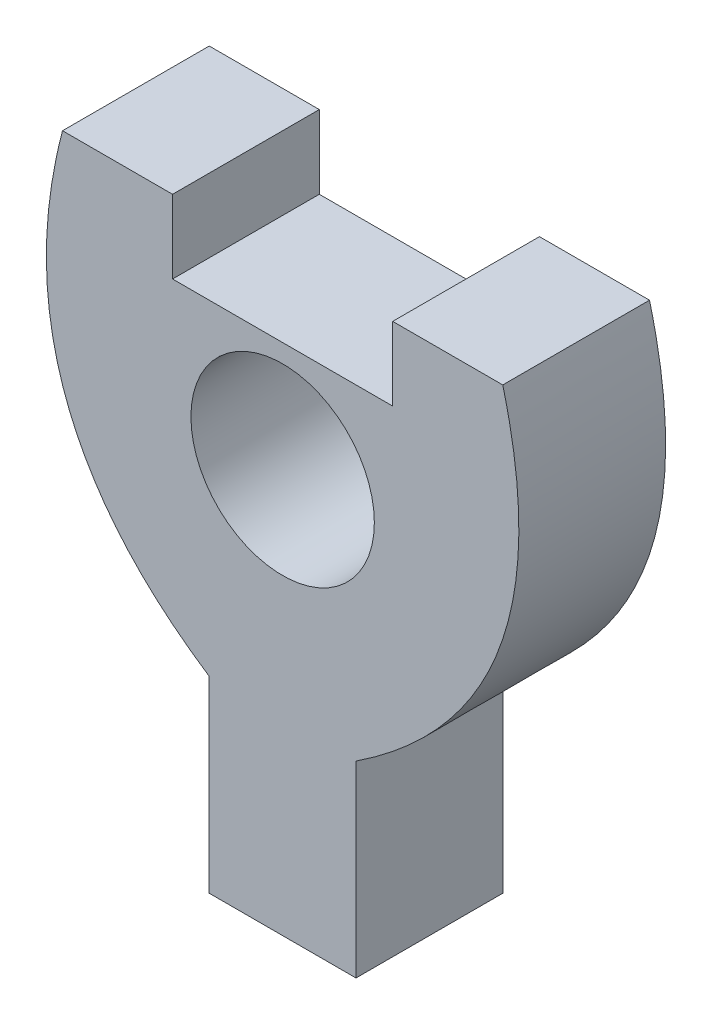
SolidWorks part; units mm, degrees
ref_plane "Front Plane" through (0, 0, 0) normal (0, 0, 1) x (1, 0, 0)
ref_plane "Top Plane" through (0, 0, 0) normal (0, 1, 0) x (1, 0, 0)
ref_plane "Right Plane" through (0, 0, 0) normal (1, 0, 0) x (0, 0, -1)
sketch "Sketch1" plane through (0, 0, 0) normal (0, 0, 1) x (1, 0, 0)
  line L0 (0, 0) -> (0, 12) construction
  line L2 (-2, 4) -> (-2, -4)
  line L3 (-2, -4) -> (2, -4)
  line L4 (2, 4) -> (2, -4)
  line L5 (-2, 4) -> (2, -4) construction
  line L6 (-2, -4) -> (2, 4) construction
  line L7 (0, 6) -> (-6, 6) construction
  line L10 (-3, 10) -> (-3, 12)
  line L12 (-6, 12) -> (-3, 12)
  line L13 (6, 12) -> (3, 12)
  line L19 (3, 12) -> (3, 10)
  line L20 (-3, 10) -> (3, 10)
  circle A0 centre (0, 7) radius 2.5
  spline S0 degree 2 poles (0, 0) (-8.1213, 3.8787) (-6, 12) knots 0 0 0 1 1 1
  spline S1 degree 2 poles (0, 0) (8.1213, 3.8787) (6, 12) knots 0 0 0 1 1 1
  point P0 (0, 0)
  dimension "D7" = 5
  dimension "D1" = 4
  dimension "D2" = 8
  dimension "D3" = 12
  dimension "D4" = 6
  dimension "D5" = 6
  dimension "D6" = 3
extrude "Boss-Extrude1" add sketch "Sketch1" along normal blind 4
